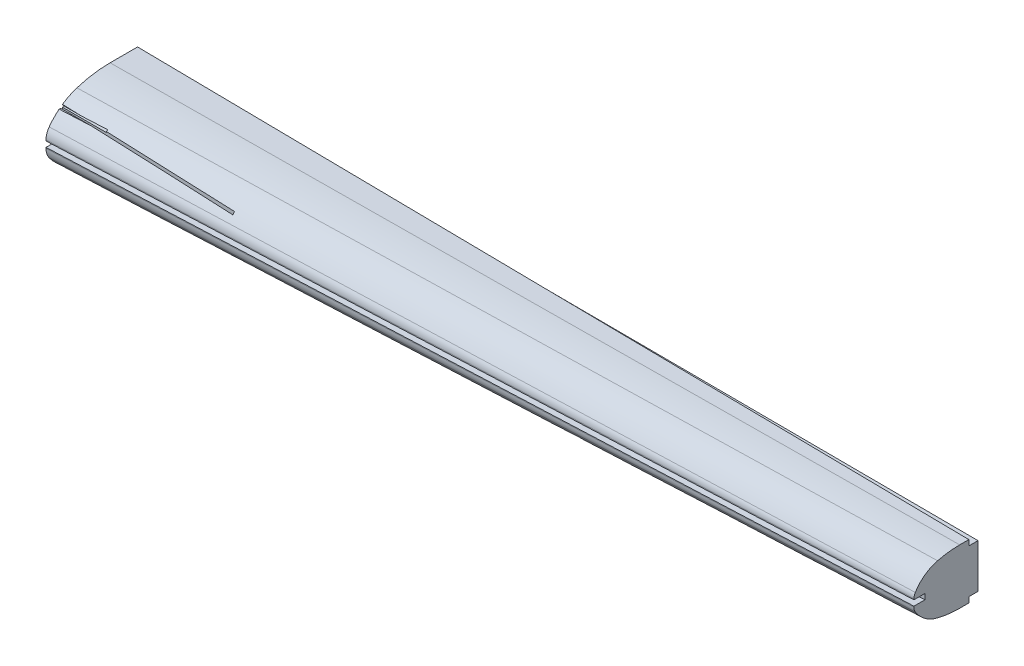
SolidWorks part; units mm, degrees
ref_plane "Front" through (0, 0, 0) normal (0, 0, 1) x (1, 0, 0)
ref_plane "Top" through (0, 0, 0) normal (0, 1, 0) x (1, 0, 0)
ref_plane "Right" through (0, 0, 0) normal (1, 0, 0) x (0, 0, -1)
sketch "Sketch1" plane through (0, 0, 0) normal (1, 0, 0) x (0, 0, -1)
  line L0 (0, 0) -> (55, 0) construction
  line L1 (55, 21) -> (55, -21)
  line L2 (55, -21) -> (35, -21)
  line L3 (55, 21) -> (35, 21)
  line L4 (0, 2) -> (0, -2)
  line L5 (1.7358, 7.3133) -> (25.9499, -10.3976) construction
  line L6 (16.8998, 18.2047) -> (35, -39) construction
  line L7 (55, 15) -> (55, -15) construction
  line L8 (55, 0) -> (20, 0) construction
  line L9 (20, -2) -> (20, 2)
  line L10 (55, 15) -> (45, 15)
  line L11 (55, -15) -> (45, -15)
  line L12 (20, 1.5) -> (26, 1.5) construction
  line L13 (26, 1.5) -> (26, 0) construction
  line L14 (26, 0) -> (26, -1.5) construction
  line L15 (26, -1.5) -> (20, -1.5) construction
  line L16 (0, 1.5) -> (6, 1.5) construction
  line L17 (6, 1.5) -> (6, 0) construction
  line L18 (6, 0) -> (6, -1.5) construction
  line L19 (6, -1.5) -> (0, -1.5) construction
  line L20 (20.7469, 4.629) -> (37.7592, -5.8869) construction
  line L21 (32.9319, 13.5218) -> (45, -35) construction
  line L22 (20, 2) -> (25, 2) construction
  line L23 (45, 15) -> (45, -35) construction
  line L24 (0, 2) -> (9, 2) construction
  line L25 (55, 14) -> (50, 14) construction
  line L26 (50, 14) -> (50, 21) construction
  line L27 (50, 15) -> (50, 12) construction
  line L28 (50, 12) -> (55, 12) construction
  line L29 (50, -15) -> (50, -12) construction
  line L30 (50, -12) -> (55, -12) construction
  line L31 (50, -21) -> (50, -14) construction
  line L32 (50, -14) -> (55, -14) construction
  arc A0 (0, 2) -> (1.7358, 7.3133) centre (9, 2) cw
  arc A1 (35, 21) -> (16.8998, 18.2047) centre (35, -39) ccw
  arc A2 (1.7358, 7.3133) -> (16.8998, 18.2047) centre (25.9499, -10.3976) cw
  arc A3 (35, -21) -> (16.8998, -18.2047) centre (35, 39) cw
  arc A4 (0, -2) -> (1.7358, -7.3133) centre (9, -2) ccw
  arc A5 (16.8998, -18.2047) -> (1.7358, -7.3133) centre (25.9499, 10.3976) cw
  arc A6 (45, 15) -> (32.9319, 13.5218) centre (45, -35) ccw
  arc A7 (20, 2) -> (20.7469, 4.629) centre (25, 2) cw
  arc A8 (20, -2) -> (20.7469, -4.629) centre (25, -2) ccw
  arc A9 (45, -15) -> (32.9319, -13.5218) centre (45, 35) cw
  arc A10 (20.7469, 4.629) -> (32.9319, 13.5218) centre (37.7592, -5.8869) cw
  arc A11 (20.7469, -4.629) -> (32.9319, -13.5218) centre (37.7592, 5.8869) ccw
  dimension "D5" = 9
  dimension "D6" = 30
  dimension "D7" = 60
  dimension "D11" = 5
  dimension "D12" = 20
  dimension "D13" = 50
  dimension "D1" = 55
  dimension "D2" = 4
  dimension "D3" = 42
  dimension "D4" = 20
  dimension "D8" = 4
  dimension "D9" = 30
  dimension "D10" = 35
  dimension "D14" = 3
  dimension "D15" = 6
  dimension "D16" = 3
  dimension "D17" = 6
  dimension "D18" = 10
  dimension "D19" = 5
  dimension "D20" = 7
  dimension "D21" = 3
  dimension "D22" = 5
sketch "Sketch2" plane through (0, 0, 0) normal (1, 0, 0) x (0, 0, -1)
  line L0 (55, 14) -> (55, -14)
  line L1 (50, -21) -> (35, -21)
  line L2 (50, 21) -> (35, 21)
  line L3 (0, 2) -> (0, 1.5)
  line L4 (0, 2) -> (9, 2) construction
  line L5 (50, 21) -> (50, 14)
  line L6 (50, 14) -> (55, 14)
  line L7 (50, -14) -> (50, -21)
  line L8 (50, -14) -> (55, -14)
  line L9 (0, 1.5) -> (6, 1.5)
  line L10 (6, 1.5) -> (6, -1.5)
  line L11 (6, -1.5) -> (0, -1.5)
  line L12 (0, -1.5) -> (0, -2)
  arc A0 (35, 21) -> (16.8998, 18.2047) centre (35, -39) ccw
  arc A1 (35, -21) -> (16.8998, -18.2047) centre (35, 39) cw
  arc A2 (16.8998, 18.2047) -> (1.7358, 7.3133) centre (25.9499, -10.3976) ccw
  arc A3 (16.8998, -18.2047) -> (1.7358, -7.3133) centre (25.9499, 10.3976) cw
  arc A4 (0, -2) -> (1.7358, -7.3133) centre (9, -2) ccw
  arc A5 (0, 2) -> (1.7358, 7.3133) centre (9, 2) cw
sketch "Sketch9" plane through (0, 0, 0) normal (0, 1, 0) x (1, 0, 0)
  line L0 (0, 0) -> (-6, 0) construction
  dimension "D1" = 6
ref_plane "Plane1" through (454, 0, 0) normal (1, 0, 0) x (0, 0, -1)
sketch "Sketch3" plane through (454, 0, 0) normal (1, 0, 0) x (0, 0, -1)
  line L0 (55, 12) -> (55, -12)
  line L1 (26, 1.5) -> (20, 1.5)
  line L2 (50, -15) -> (45, -15)
  line L3 (20, 2) -> (20, 1.5)
  line L4 (45, 15) -> (50, 15)
  line L5 (50, 15) -> (50, 12)
  line L6 (50, 12) -> (55, 12)
  line L7 (55, -12) -> (50, -12)
  line L8 (50, -12) -> (50, -15)
  line L9 (20, -1.5) -> (20, -2)
  line L10 (26, 1.5) -> (26, -1.5)
  line L11 (26, -1.5) -> (20, -1.5)
  arc A0 (20, 2) -> (20.7469, 4.629) centre (25, 2) cw
  arc A1 (20, -2) -> (20.7469, -4.629) centre (25, -2) ccw
  arc A2 (45, 15) -> (32.9319, 13.5218) centre (45, -35) ccw
  arc A3 (45, -15) -> (32.9319, -13.5218) centre (45, 35) cw
  arc A4 (32.9319, 13.5218) -> (20.7469, 4.629) centre (37.7592, -5.8869) ccw
  arc A5 (32.9319, -13.5218) -> (20.7469, -4.629) centre (37.7592, 5.8869) cw
ref_plane "Plane2" through (484, 0, 0) normal (1, 0, 0) x (0, 0, -1)
sketch "Sketch8" plane through (0, 0, 0) normal (1, 0, 0) x (0, 0, -1)
  line L0 (35, 21) -> (50, 21)
  line L1 (50, 21) -> (50, 14)
  line L2 (50, 14) -> (55, 14)
  line L3 (55, 14) -> (55, -14)
  line L4 (55, -14) -> (50, -14)
  line L5 (50, -14) -> (50, -21)
  line L6 (50, -21) -> (35, -21)
  line L7 (0, 2) -> (0, 1.5)
  line L8 (0, 1.5) -> (6, 1.5)
  line L9 (6, 1.5) -> (6, -1.5)
  line L10 (6, -1.5) -> (0, -1.5)
  line L11 (0, -1.5) -> (0, -2)
  arc A0 (35, 21) -> (16.8998, 18.2047) centre (35, -39) ccw
  arc A1 (35, -21) -> (16.8998, -18.2047) centre (35, 39) cw
  arc A2 (16.8998, 18.2047) -> (1.7358, 7.3133) centre (25.9499, -10.3976) ccw
  arc A3 (16.8998, -18.2047) -> (1.7358, -7.3133) centre (25.9499, 10.3976) cw
  arc A4 (1.7358, 7.3133) -> (0, 2) centre (9, 2) ccw
  arc A5 (1.7358, -7.3133) -> (0, -2) centre (9, -2) cw
sketch "Sketch7" plane through (484, 0, 0) normal (1, 0, 0) x (0, 0, -1)
  line L0 (20, 2) -> (20, 1.5)
  line L1 (50, 15) -> (45, 15)
  line L2 (55, 12) -> (55, -12)
  line L3 (50, -15) -> (45, -15)
  line L4 (20, 1.5) -> (26, 1.5)
  line L5 (26, 1.5) -> (26, -1.5)
  line L6 (26, -1.5) -> (20, -1.5)
  line L7 (55, 12) -> (50, 12)
  line L8 (50, 15) -> (50, 12)
  line L9 (20, -1.5) -> (20, -2)
  line L11 (55, -12) -> (50, -12)
  line L12 (50, -15) -> (50, -12)
  arc A0 (45, 15) -> (32.9319, 13.5218) centre (45, -35) ccw
  arc A1 (45, -15) -> (32.9319, -13.5218) centre (45, 35) cw
  arc A2 (32.9319, 13.5218) -> (20.7469, 4.629) centre (37.7592, -5.8869) ccw
  arc A3 (32.9319, -13.5218) -> (20.7469, -4.629) centre (37.7592, 5.8869) cw
  arc A4 (20.7469, 4.629) -> (20, 2) centre (25, 2) ccw
  arc A5 (20.7469, -4.629) -> (20, -2) centre (25, -2) cw
loft "Loft1" add profiles "Sketch2", "Sketch3"
loft "Loft2" add profiles "Sketch8", "Sketch7"
sketch "Sketch4" plane through (0, 0, 0) normal (1, 0, 0) x (0, 0, -1)
  line L0 (55, -14) -> (55, 14) construction
  line L1 (55, 13) -> (0, 13)
  line L2 (55, 13) -> (55, 14)
  line L3 (55, 14) -> (0, 14)
  line L4 (0, 13) -> (0, 14)
  line L5 (55, -14) -> (0, -14)
  line L6 (55, -14) -> (55, -13)
  line L7 (55, -13) -> (0, -13)
  line L8 (0, -14) -> (0, -13)
  line L9 (0, 13) -> (0, -13) construction
  dimension "D1" = 1
  dimension "D2" = 28
extrude "Cut-Extrude1" cut sketch "Sketch4" along normal blind 24
sketch "Sketch5" plane through (0, 0, 0) normal (1, 0, 0) x (0, 0, -1)
  line L0 (7.1736, 13) -> (55, 13) construction
  line L1 (9, 13) -> (8, 13) construction
  line L2 (9, 13) -> (9, -13)
  line L3 (9, -13) -> (8, -13) construction
  line L4 (8, 13) -> (8, -13)
  line L5 (55, -13) -> (7.1736, -13) construction
  line L6 (9, -13) -> (9, -17.5)
  line L7 (9, -17.5) -> (8, -17.5)
  line L8 (8, -17.5) -> (8, -13)
  line L9 (9, 13) -> (9, 17.5)
  line L10 (9, 17.5) -> (8, 17.5)
  line L11 (8, 17.5) -> (8, 13)
  dimension "D1" = 1
  dimension "D2" = 8
  dimension "D3" = 35
extrude "Cut-Extrude2" cut sketch "Sketch5" along normal blind 94
